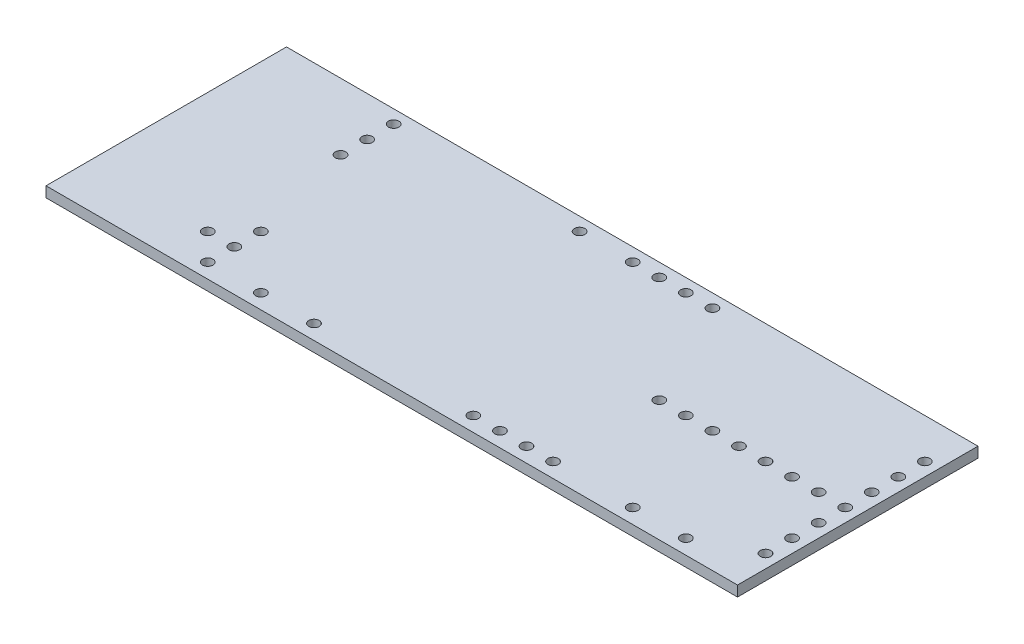
SolidWorks part; units mm, degrees
ref_plane "Front Plane" through (0, 0, 0) normal (0, 0, 1) x (1, 0, 0)
ref_plane "Top Plane" through (0, 0, 0) normal (0, 1, 0) x (1, 0, 0)
ref_plane "Right Plane" through (0, 0, 0) normal (1, 0, 0) x (0, 0, -1)
sketch "Sketch1" plane through (0, 0, 0) normal (0, 1, 0) x (1, 0, 0)
  line L1 (0, 0) -> (58.5, 0)
  line L2 (0, 0) -> (0, -23)
  line L3 (0, -23) -> (58.5, -23)
  line L4 (58.5, 0) -> (58.5, -23)
  dimension "D1" = 58.5
  dimension "D2" = 23
extrude "Boss-Extrude1" add sketch "Sketch1" along normal blind 1
sketch "Sketch2" plane through (0, 1, 0) normal (0, 1, 0) x (1, 0, 0)
  line L0 (58.5, -23) -> (58.5, 0) construction
  line L1 (58.5, 0) -> (0, 0) construction
  circle A0 centre (57.23, -3.81) radius 0.5
  circle A1 centre (57.23, -6.35) radius 0.5
  circle A2 centre (57.23, -8.89) radius 0.5
  circle A3 centre (57.23, -11.43) radius 0.5
  circle A4 centre (57.23, -13.97) radius 0.5
  circle A5 centre (57.23, -16.51) radius 0.5
  circle A6 centre (57.23, -19.05) radius 0.5
  circle A7 centre (54.69, -11.43) radius 0.5
  circle A8 centre (52.15, -11.43) radius 0.5
  circle A9 centre (49.61, -11.43) radius 0.5
  circle A10 centre (47.07, -11.43) radius 0.5
  circle A11 centre (44.53, -11.43) radius 0.5
  circle A12 centre (41.99, -11.43) radius 0.5
  circle A13 centre (39.45, -11.43) radius 0.5
  circle A14 centre (39.45, -13.97) radius 0.5 [skipped]
  circle A15 centre (39.45, -16.51) radius 0.5 [skipped]
  circle A16 centre (39.45, -19.05) radius 0.5 [skipped]
  circle A17 centre (39.45, -21.59) radius 0.5
  circle A18 centre (36.91, -21.59) radius 0.5
  circle A19 centre (34.37, -21.59) radius 0.5
  circle A20 centre (31.83, -21.59) radius 0.5
  circle A21 centre (29.29, -21.59) radius 0.5 [skipped]
  circle A22 centre (26.75, -21.59) radius 0.5 [skipped]
  circle A23 centre (24.21, -21.59) radius 0.5 [skipped]
  circle A24 centre (21.67, -21.59) radius 0.5 [skipped]
  circle A25 centre (19.13, -21.59) radius 0.5 [skipped]
  circle A26 centre (16.59, -21.59) radius 0.5
  circle A27 centre (14.05, -21.59) radius 0.5 [skipped]
  circle A28 centre (11.51, -21.59) radius 0.5
  circle A29 centre (8.97, -21.59) radius 0.5 [skipped]
  circle A30 centre (6.43, -21.59) radius 0.5
  circle A31 centre (41.99, -21.59) radius 0.5 [skipped]
  circle A32 centre (44.53, -21.59) radius 0.5 [skipped]
  circle A33 centre (47.07, -21.59) radius 0.5
  circle A34 centre (49.61, -21.59) radius 0.5 [skipped]
  circle A35 centre (52.15, -21.59) radius 0.5
  circle A36 centre (6.43, -19.05) radius 0.5
  circle A37 centre (6.43, -16.51) radius 0.5
  circle A38 centre (3.89, -19.05) radius 0.5
  circle A39 centre (3.89, -16.51) radius 0.5 [skipped]
  circle A40 centre (3.89, -13.97) radius 0.5 [skipped]
  circle A41 centre (3.89, -11.43) radius 0.5 [skipped]
  circle A42 centre (3.89, -8.89) radius 0.5 [skipped]
  circle A43 centre (3.89, -6.35) radius 0.5
  circle A44 centre (3.89, -3.81) radius 0.5
  circle A45 centre (3.89, -1.27) radius 0.5
  circle A46 centre (6.43, -1.27) radius 0.5 [skipped]
  circle A47 centre (8.97, -1.27) radius 0.5 [skipped]
  circle A48 centre (11.51, -1.27) radius 0.5 [skipped]
  circle A49 centre (14.05, -1.27) radius 0.5 [skipped]
  circle A50 centre (16.59, -1.27) radius 0.5 [skipped]
  circle A51 centre (19.13, -1.27) radius 0.5 [skipped]
  circle A52 centre (21.67, -1.27) radius 0.5
  circle A53 centre (24.21, -1.27) radius 0.5 [skipped]
  circle A54 centre (26.75, -1.27) radius 0.5
  circle A55 centre (29.29, -1.27) radius 0.5
  circle A56 centre (31.83, -1.27) radius 0.5
  circle A57 centre (34.37, -1.27) radius 0.5
  dimension "D1" = 1
  dimension "D2" = 1.27
  dimension "D3" = 3.81
  dimension "D4" = 7
  dimension "D5" = 8
  dimension "D6" = 5
  dimension "D7" = 14
  dimension "D8" = 6
  dimension "D9" = 3
  dimension "D10" = 2
  dimension "D11" = 8
  dimension "D12" = 13
extrude "Cut-Extrude1" cut sketch "Sketch2" against normal through all contours A26 | A28 | A30 | A36 | A38 | A37 | A43 | A44 | A45 | A52 | A54 | A55 | A56 | A57 | A13 | A20 | A19 | A18 | A17 | A12 | A11 | A10 | A9 | A33 | A8 | A7 | A35 | A6 | A5 | A4 | A3 | A2 | A1 | A0
sketch "Sketch3" plane through (0, 0, 0) normal (-1, 0, 0) x (0, 0, 1)
  line L4 (0, 0) -> (23, 0)
  line L5 (23, 0) -> (23, 1)
  line L6 (23, 1) -> (0, 1)
  line L7 (0, 1) -> (0, 0)
  line L8 (0, 0) -> (23, 0)
  line L9 (23, 0) -> (23, 1)
  line L10 (23, 1) -> (0, 1)
  line L11 (0, 1) -> (0, 0)
  dimension "D1" = 0
extrude "Boss-Extrude2" add sketch "Sketch3" along normal blind 7.63
